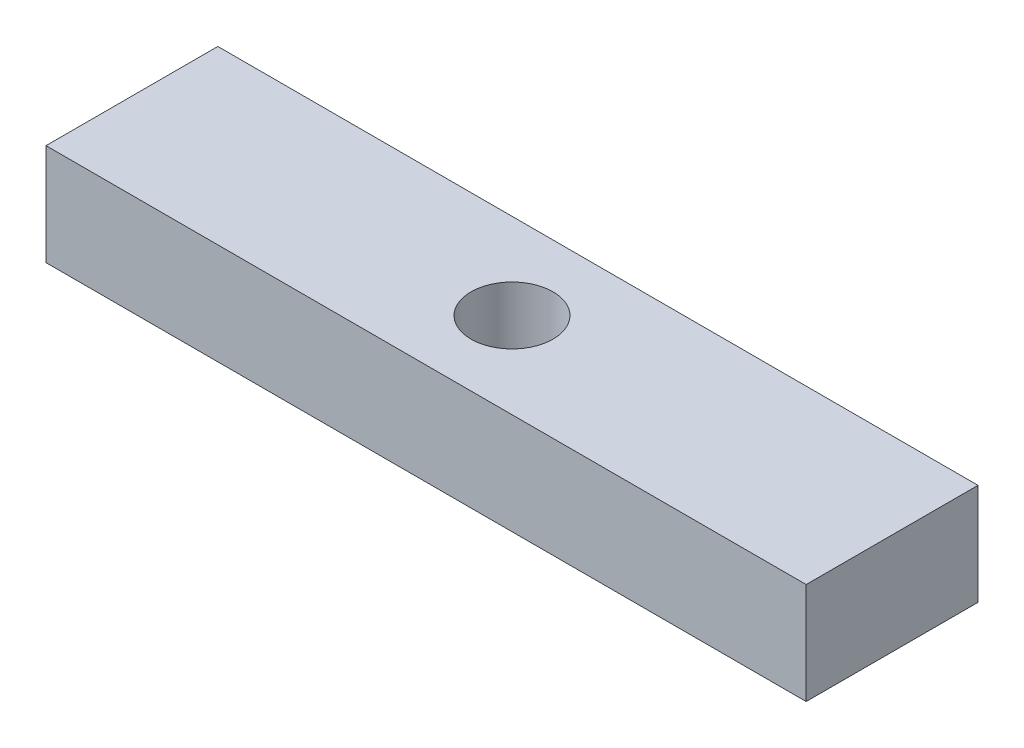
SolidWorks part; units mm, degrees
ref_plane "Front Plane" through (0, 0, 0) normal (0, 0, 1) x (1, 0, 0)
ref_plane "Top Plane" through (0, 0, 0) normal (0, 1, 0) x (1, 0, 0)
ref_plane "Right Plane" through (0, 0, 0) normal (1, 0, 0) x (0, 0, -1)
sketch "Sketch1" plane through (0, 0, 0) normal (0, 1, 0) x (1, 0, 0)
  line L1 (-20.0025, -4.5212) -> (20.0025, -4.5212)
  line L2 (-20.0025, -4.5212) -> (-20.0025, 4.5212)
  line L3 (-20.0025, 4.5212) -> (20.0025, 4.5212)
  line L4 (20.0025, -4.5212) -> (20.0025, 4.5212)
  line L5 (-20.0025, -4.5212) -> (20.0025, 4.5212) construction
  line L6 (-20.0025, 4.5212) -> (20.0025, -4.5212) construction
  point P0 (0, 0)
  dimension "D1" = 40.005
  dimension "D2" = 9.0424
extrude "Boss-Extrude1" add sketch "Sketch1" along normal blind 5.334
sketch "Sketch2" plane through (0, 5.334, 0) normal (0, 1, 0) x (1, 0, 0)
  circle A0 centre (0, 0) radius 2.159
  dimension "D1" = 4.318
extrude "Cut-Extrude1" cut sketch "Sketch2" against normal through all
